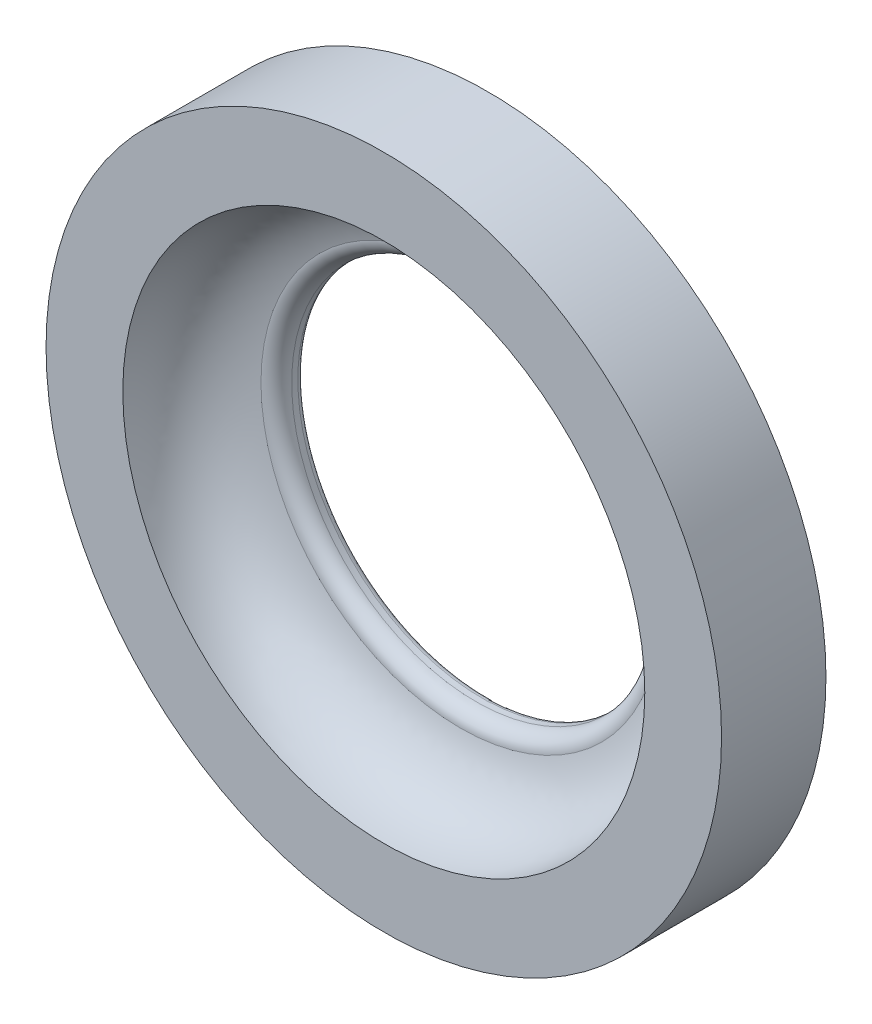
SolidWorks part; units mm, degrees
ref_plane "Front Plane" through (0, 0, 0) normal (0, 0, 1) x (1, 0, 0)
ref_plane "Top Plane" through (0, 0, 0) normal (0, 1, 0) x (1, 0, 0)
ref_plane "Right Plane" through (0, 0, 0) normal (1, 0, 0) x (0, 0, -1)
sketch "Sketch2" plane through (0, 0, 0) normal (0, 1, 0) x (1, 0, 0)
  line L0 (0, 0) -> (-2.5156, 0) construction
  line L1 (0, 0) -> (0, 2.2186) construction
  line L2 (-5.5, 0) -> (-5.5, 1.7)
  line L3 (-5.5, 1.7) -> (-3.1, 1.7)
  line L4 (-3, 1.6) -> (-3, 1.5)
  line L6 (-5.5, 0) -> (-4.25, 0)
  arc A0 (-3.25, 1.25) -> (-3, 1.5) centre (-3.25, 1.5) ccw
  arc A1 (-3.1, 1.7) -> (-3, 1.6) centre (-3.1, 1.6) cw
  spline S0 degree 2 poles (-4.25, 0) (-4.2268, 1.0055) (-3.25, 1.25) knots 0 0 0 1 1 1
  point P11 (-3, 1.7)
  dimension "D5" = 0.25
  dimension "D7" = 0.1
  dimension "D1" = 1.7
  dimension "D2" = 4.25
  dimension "D3" = 5.5
  dimension "D4" = 3
  dimension "D6" = 0.2
revolve "Revolve1" add sketch "Sketch2" angle 360 about L1
